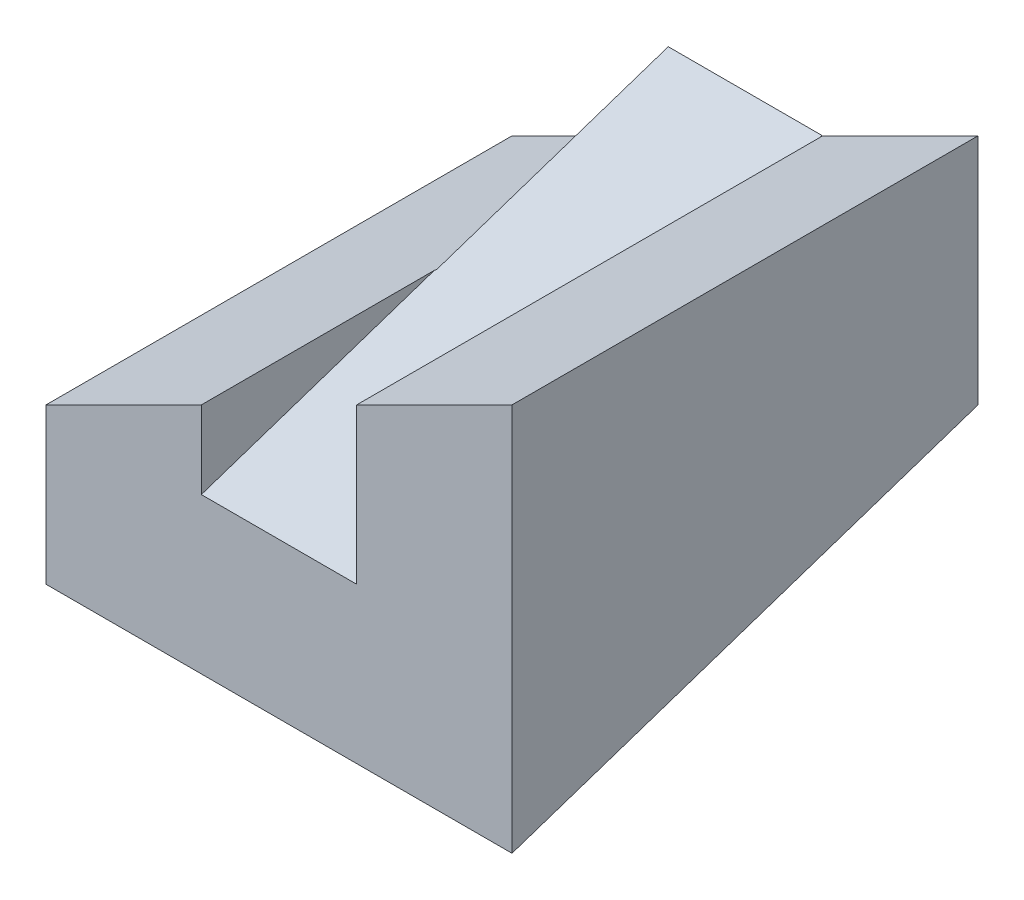
SolidWorks part; units mm, degrees
ref_plane "Front" through (0, 0, 0) normal (0, 0, 1) x (1, 0, 0)
ref_plane "Top" through (0, 0, 0) normal (0, 1, 0) x (1, 0, 0)
ref_plane "Right" through (0, 0, 0) normal (1, 0, 0) x (0, 0, -1)
sketch "Sketch1" plane through (0, 0, 0) normal (0, 1, 0) x (1, 0, 0)
  line L1 (-3, -3) -> (3, -3)
  line L2 (-3, -3) -> (-3, 3)
  line L3 (-3, 3) -> (3, 3)
  line L4 (3, -3) -> (3, 3)
  line L5 (-3, -3) -> (3, 3) construction
  line L6 (-3, 3) -> (3, -3) construction
  point P0 (0, 0)
  dimension "D1" = 6
  dimension "D2" = 6
extrude "Boss-Extrude1" add sketch "Sketch1" along normal blind 5
sketch "Sketch11" plane through (0, 0, 3) normal (0, 0, 1) x (1, 0, 0)
  line L0 (-3, 2) -> (3, 5)
  line L2 (-0.9881, 2) -> (0.9881, 2)
  line L3 (-0.9881, 2) -> (-0.9881, 4)
  line L4 (-3, 0) -> (3, 0)
  line L5 (3, 0) -> (3, 5)
  line L6 (3, 5) -> (-3, 5)
  line L7 (-3, 5) -> (-3, 0)
  line L8 (-3, 0) -> (3, 0)
  line L9 (3, 0) -> (3, 5)
  line L10 (3, 5) -> (-3, 5)
  line L11 (-3, 5) -> (-3, 0)
  line L12 (-0.9881, 4) -> (0.9881, 4)
  line L13 (0.9881, 2) -> (0.9881, 4)
  line L14 (-0.9881, 2) -> (0.9881, 4) construction
  line L15 (-0.9881, 4) -> (0.9881, 2) construction
  point P5 (0, 3)
  line M8 (3, 5) -> (-3, 5)
  line M9 (-3, 5) -> (-3, 0)
  dimension "D2" = 3
  dimension "D3" = 3
  dimension "D4" = 2
  dimension "D1" = 0
extrude "Cut-Extrude12" cut sketch "Sketch11" against normal blind 12 contours L13 L0 L3 L12 M8 M9
sketch "Sketch12" plane through (0, 0, 0) normal (1, 0, 0) x (0, 0, -1)
  line L0 (3, 2) -> (-3, 2) construction
  line L1 (-3, 2) -> (-3, 3.006) construction
  line L2 (3, 3.006) -> (3, 2) construction
  line L3 (-3, 3.006) -> (-3, 4) construction
  line L4 (-3, 4) -> (3, 4) construction
  line L5 (3, 4) -> (3, 3.006) construction
  line L6 (3, 2) -> (-3, 2)
  line L7 (-3, 2) -> (-3, 3.006)
  line L8 (3, 3.006) -> (3, 2)
  line L9 (-3, 3.006) -> (-3, 4)
  line L10 (-3, 4) -> (3, 4)
  line L11 (3, 4) -> (3, 3.006)
  line L12 (3, 4) -> (-3, 2)
extrude "Cut-Extrude13" cut sketch "Sketch12" against normal mid plane 2 contours L12 L10 L9 L7
sketch "Sketch13" plane through (3, 0, 0) normal (1, 0, 0) x (0, 0, -1)
  line L0 (-3, 0) -> (3, 2)
  line L1 (3, 2) -> (3, 0)
  line L4 (-3, 0) -> (3, 0)
  line L5 (3, 0) -> (3, 5)
  line L6 (3, 5) -> (-3, 5)
  line L7 (-3, 5) -> (-3, 0)
  line L8 (-3, 0) -> (3, 0)
  line L9 (3, 0) -> (3, 5)
  line L10 (3, 5) -> (-3, 5)
  line L11 (-3, 5) -> (-3, 0)
  line M6 (-3, 0) -> (3, 0)
  line M7 (3, 0) -> (3, 5)
  dimension "D2" = 2
  dimension "D1" = 0
extrude "Cut-Extrude14" cut sketch "Sketch13" against normal blind 2 contours L0 M6 M7
